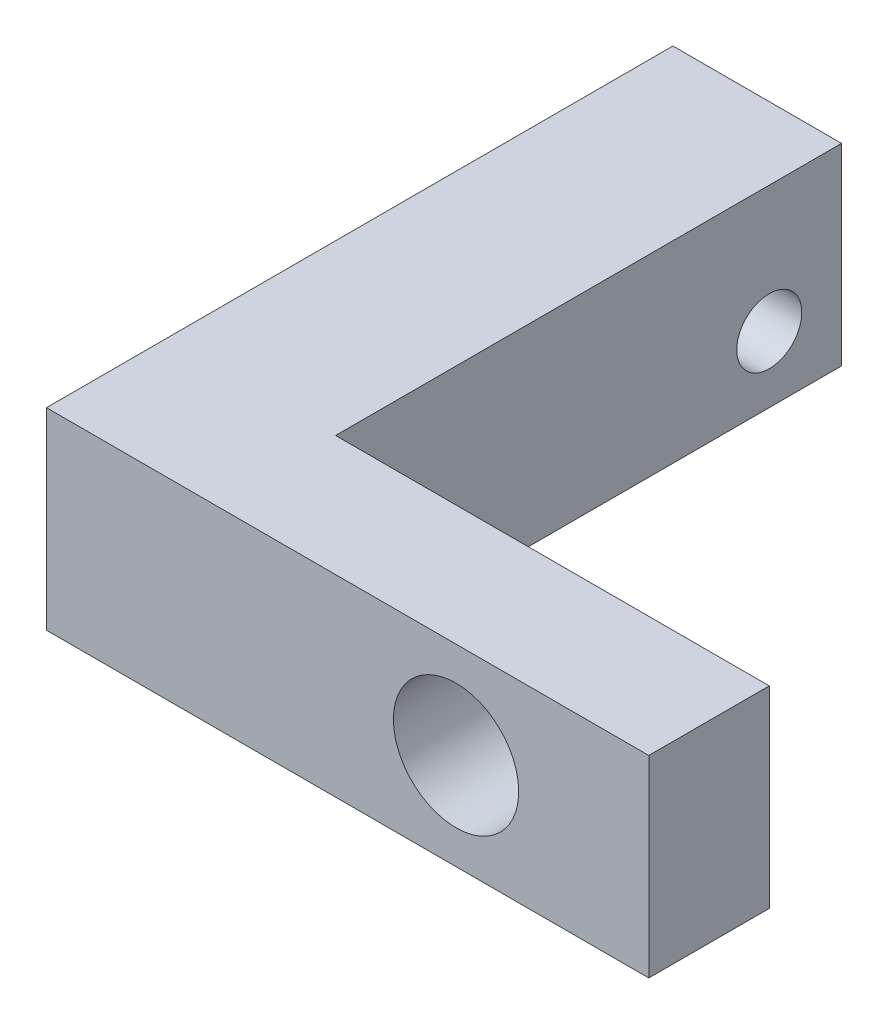
SolidWorks part; units mm, degrees
material "ABS"
ref_plane "Front Plane" through (0, 0, 0) normal (0, 0, 1) x (1, 0, 0)
ref_plane "Top Plane" through (0, 0, 0) normal (0, 1, 0) x (1, 0, 0)
ref_plane "Right Plane" through (0, 0, 0) normal (1, 0, 0) x (0, 0, -1)
sketch "Sketch1" plane through (0, 0, 0) normal (0, 1, 0) x (1, 0, 0)
  line L0 (0, 0) -> (0, 26)
  line L1 (0, 26) -> (7, 26)
  line L2 (7, 26) -> (7, 5)
  line L3 (7, 5) -> (25, 5)
  line L4 (25, 5) -> (25, 0)
  line L5 (25, 0) -> (0, 0)
  dimension "D1" = 26
  dimension "D2" = 25
  dimension "D3" = 5
  dimension "D4" = 7
extrude "Boss-Extrude1" add sketch "Sketch1" along normal blind 8
sketch "Sketch2" plane through (0, 0, 0) normal (-1, 0, 0) x (0, 0, 1)
  line L0 (-26, 8) -> (-26, 0) construction
  line L2 (-5, 0) -> (-26, 0) construction
  circle A0 centre (-23, 2.75) radius 1.35
  circle A1 centre (-3.5, 2.75) radius 1.35
  dimension "D2" = 2.7
  dimension "D3" = 3
  dimension "D4" = 2.75
  dimension "D1" = 19.5
extrude "Cut-Extrude1" cut sketch "Sketch2" against normal blind 10
sketch "Sketch4" plane through (0, 0, -5) normal (0, 0, -1) x (-1, 0, 0)
  line L0 (-17, 8) -> (-17, 0) construction
  line L1 (-25, 8) -> (-7, 8) construction
  line L2 (-25, 0) -> (-7, 0) construction
  line L6 (-7, 8) -> (-7, 0) construction
  circle A0 centre (-17, 4) radius 2.6
  dimension "D1" = 5.2
  dimension "D2" = 10
extrude "Cut-Extrude2" cut sketch "Sketch4" against normal up to next
